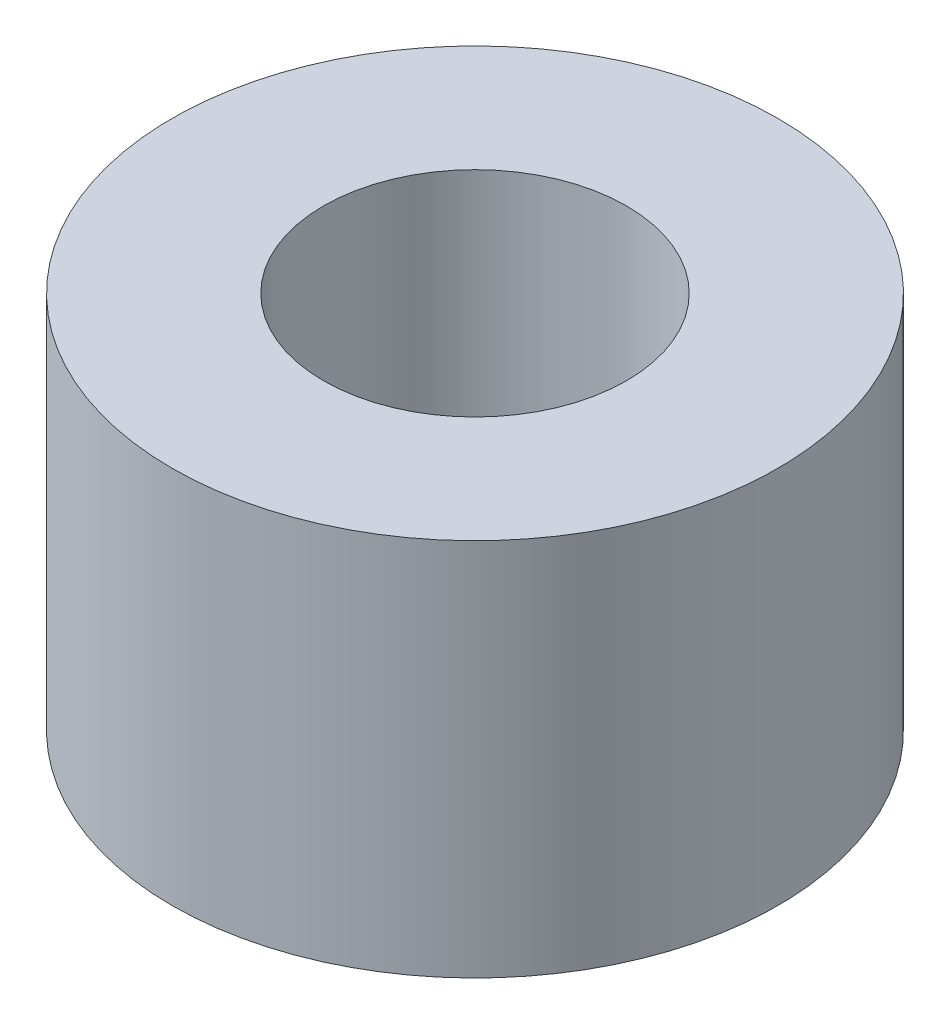
SolidWorks part; units mm, degrees
ref_plane "Front Plane" through (0, 0, 0) normal (0, 0, 1) x (1, 0, 0)
ref_plane "Top Plane" through (0, 0, 0) normal (0, 1, 0) x (1, 0, 0)
ref_plane "Right Plane" through (0, 0, 0) normal (1, 0, 0) x (0, 0, -1)
sketch "Sketch1" plane through (0, 0, 0) normal (0, 1, 0) x (1, 0, 0)
  circle A0 centre (0, 0) radius 2
  circle A1 centre (0, 0) radius 4
  dimension "D1" = 4
  dimension "D2" = 8
extrude "Boss-Extrude1" add sketch "Sketch1" along normal blind 5
